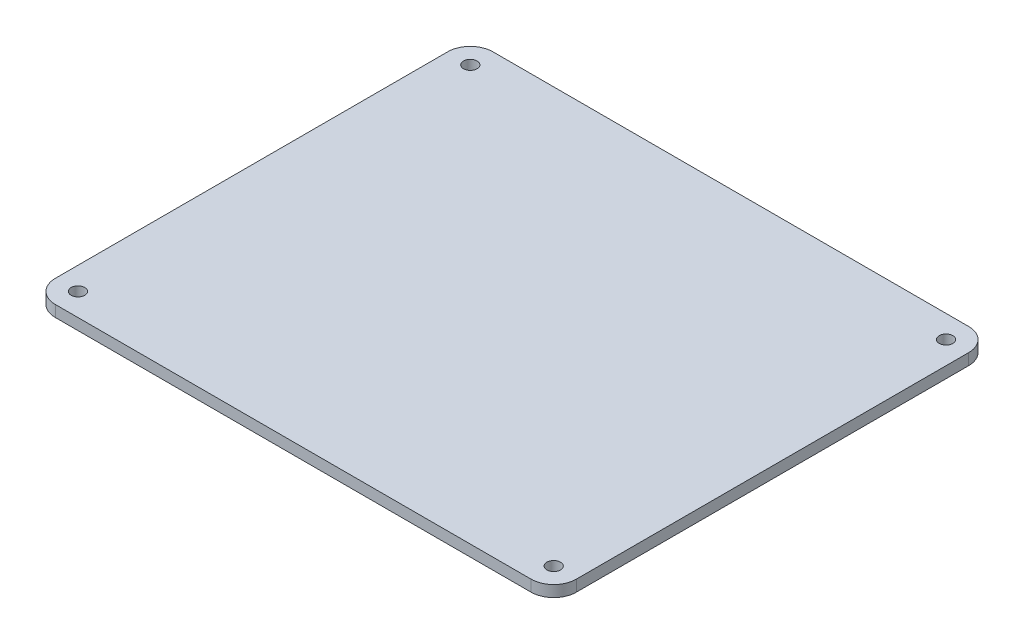
SolidWorks part; units mm, degrees
ref_plane "前视基准面" through (0, 0, 0) normal (0, 0, 1) x (1, 0, 0)
ref_plane "上视基准面" through (0, 0, 0) normal (0, 1, 0) x (1, 0, 0)
ref_plane "右视基准面" through (0, 0, 0) normal (1, 0, 0) x (0, 0, -1)
sketch "草图1" plane through (0, 24.6371, 0) normal (0, 1, 0) x (1, 0, 0)
  line L1 (-135.6304, 34.9177) -> (-30.5685, 34.9177)
  line L2 (-140.6304, 29.9177) -> (-140.6304, -56.7273)
  line L3 (-135.6304, -61.7273) -> (-30.5685, -61.7273)
  line L4 (-25.5685, 29.9177) -> (-25.5685, -56.7273)
  arc A4 (-140.6304, 29.9177) -> (-135.6304, 34.9177) centre (-135.6304, 29.9177) cw
  arc A5 (-25.5685, 29.9177) -> (-30.5685, 34.9177) centre (-30.5685, 29.9177) ccw
  arc A6 (-25.5685, -56.7273) -> (-30.5685, -61.7273) centre (-30.5685, -56.7273) cw
  arc A7 (-135.6304, -61.7273) -> (-140.6304, -56.7273) centre (-135.6304, -56.7273) cw
  circle A8 centre (-135.6304, 29.9177) radius 1.5
  circle A9 centre (-30.5685, 29.9177) radius 1.5
  circle A10 centre (-30.5685, -56.7273) radius 1.5
  circle A11 centre (-135.6304, -56.7273) radius 1.5
  dimension "D1" = 5
extrude "凸台-拉伸1" add sketch "草图1" along normal blind 2.5
